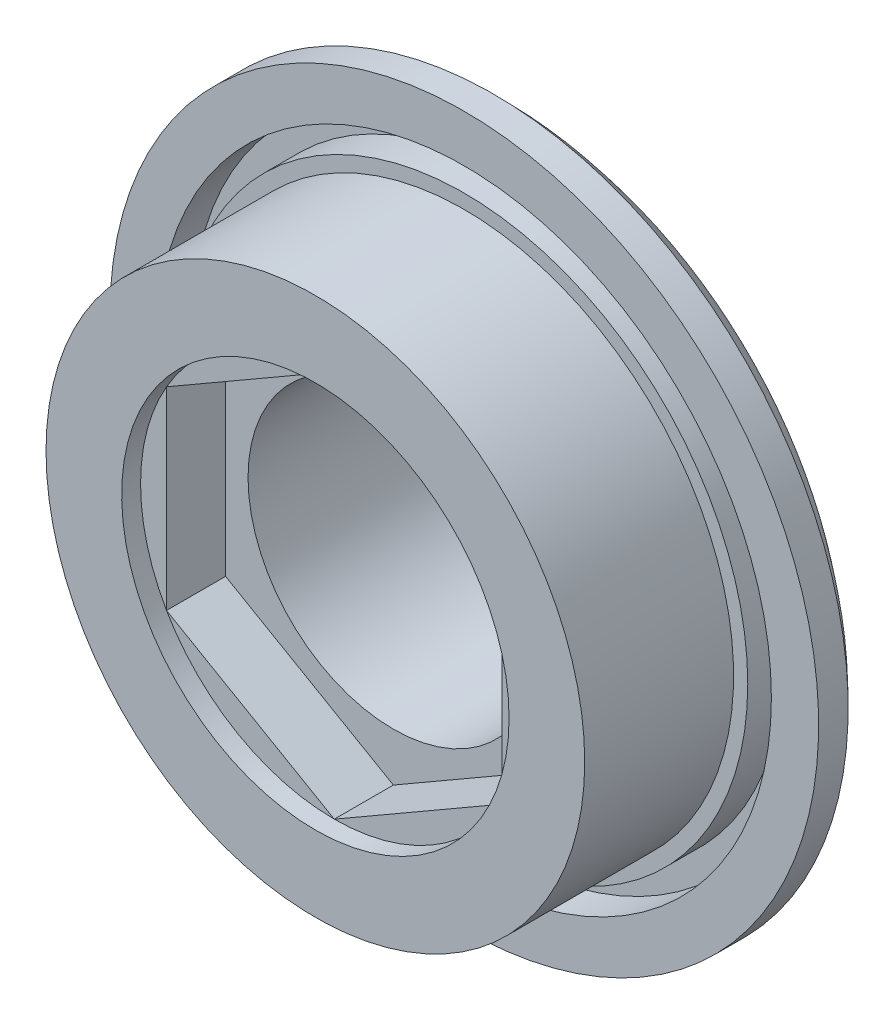
SolidWorks part; units mm, degrees
ref_plane "Front Plane" through (0, 0, 0) normal (0, 0, 1) x (1, 0, 0)
ref_plane "Top Plane" through (0, 0, 0) normal (0, 1, 0) x (1, 0, 0)
ref_plane "Right Plane" through (0, 0, 0) normal (1, 0, 0) x (0, 0, -1)
sketch "Sketch1" plane through (0, 0, 0) normal (0, 1, 0) x (1, 0, 0)
  line L0 (0, 0) -> (0, -14.25) construction
  line L1 (6.15, -14.25) -> (6.15, 0)
  line L2 (15, -4.25) -> (15, -3)
  line L3 (11.4, -14.25) -> (6.15, -14.25)
  line L4 (6.15, 0) -> (0, 0) construction
  line L5 (6.15, -14.25) -> (0, -14.25) construction
  line L6 (15, -4.25) -> (11.4, -4.25)
  line L7 (11.4, -4.25) -> (11.4, -14.25)
  line L8 (6.15, 0) -> (8, 0)
  arc A1 (8, 0) -> (15, -3) centre (8, -9.6667) cw
  point P10 (7.2525, 0)
  dimension "D1" = 6.15
  dimension "D2" = 11.4
  dimension "D3" = 14.25
  dimension "D4" = 3
  dimension "D5" = 8
  dimension "D6" = 15
  dimension "D7" = 10
revolve "Revolve1" add sketch "Sketch1" angle 360 about L0
sketch "Sketch3" plane through (0, 0, 14.25) normal (0, 0, 1) x (1, 0, 0)
  line L1 (0, -8.1984) -> (7.1, -4.0992)
  line L2 (7.1, -4.0992) -> (7.1, 4.0992)
  line L3 (7.1, 4.0992) -> (0, 8.1984)
  line L4 (0, 8.1984) -> (-7.1, 4.0992)
  line L5 (-7.1, 4.0992) -> (-7.1, -4.0992)
  line L6 (-7.1, -4.0992) -> (0, -8.1984)
  circle A0 centre (0, 0) radius 7.1 construction
  circle A1 centre (0, 0) radius 11.4 construction
  point P1 (0.4957, 0.0324)
  point P9 (0, 0)
  dimension "D1" = 14.2
extrude "Cut-Extrude2" cut sketch "Sketch3" against normal offset from surface (7 mm away) 7.25 up to face at (-6.15, 0, 0)
sketch "Sketch2" plane through (0, 0, 14.25) normal (0, 0, 1) x (1, 0, 0)
  circle A2 centre (0, 0) radius 13
  dimension "D1" = 26
extrude "Cut-Extrude1" cut sketch "Sketch2" against normal offset from surface (4.5 mm away) 9.75 up to face at (-6.15, 0, 0)
sketch "Sketch5" plane through (0, 0, 9.75) normal (0, 0, 1) x (1, 0, 0)
  circle A0 centre (0, 0) radius 11.4
  circle A1 centre (0, 0) radius 8.1984
  circle A2 centre (0, 0) radius 11.4 construction
extrude "Boss-Extrude2" add sketch "Sketch5" along normal blind 0.8
sketch "Sketch6" plane through (0, 0, 4.25) normal (0, 0, 1) x (1, 0, 0)
  circle A0 centre (0, 0) radius 11 construction
  circle A1 centre (0, 0) radius 12
  circle A2 centre (0, 0) radius 13
  dimension "D1" = 1
  dimension "D2" = 1
extrude "Cut-Extrude3" cut sketch "Sketch6" against normal blind 1.5
